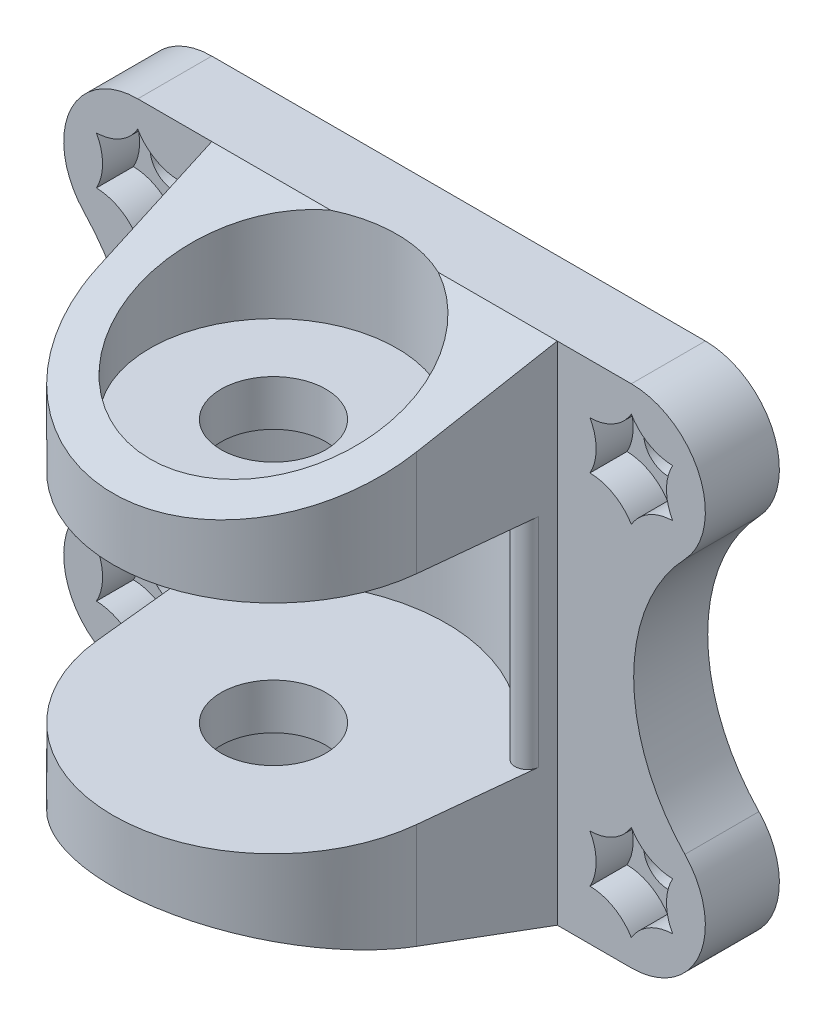
SolidWorks part; units mm, degrees
ref_plane "Front Plane" through (0, 0, 0) normal (0, 0, 1) x (1, 0, 0)
ref_plane "Top Plane" through (0, 0, 0) normal (0, 1, 0) x (1, 0, 0)
ref_plane "Right Plane" through (0, 0, 0) normal (1, 0, 0) x (0, 0, -1)
sketch "Sketch1" plane through (0, 0, 0) normal (0, 1, 0) x (1, 0, 0)
  line L0 (-12.931, -1.3372) -> (-14, 9)
  line L1 (-14, 9) -> (-14, 15)
  line L2 (-14, 15) -> (14, 15)
  line L3 (12.931, -1.3372) -> (14, 9)
  line L4 (14, 9) -> (14, 15)
  circle A0 centre (0, 0) radius 4.25
  arc A1 (-12.931, -1.3372) -> (12.931, -1.3372) centre (0, 0) ccw
  dimension "D1" = 8.5
  dimension "D3" = 13
  dimension "D2" = 15
  dimension "D4" = 28
  dimension "D5" = 6
extrude "Boss-Extrude1" add sketch "Sketch1" along normal mid plane 41
sketch "Sketch2" plane through (0, 0, 0) normal (1, 0, 0) x (0, 0, -1)
  line L0 (0, 0) -> (0, 31.6961) construction
  line L2 (-14, 8.8) -> (0, 8.8)
  line L3 (-14, 8.8) -> (-14, -8.8)
  line L4 (-14, -8.8) -> (0, -8.8)
  line L5 (0, 8.8) -> (0, -8.8)
  dimension "D1" = 17.6
  dimension "D2" = 28
revolve "Cut-Revolve1" cut sketch "Sketch2" angle 360 about L0
sketch "Sketch3" plane through (14, 0, 0) normal (1, 0, 0) x (0, 0, -1)
  line L0 (9, 20.5) -> (-13, 13.8)
  line L1 (-13, 13.8) -> (-13, 20.5)
  line L2 (-13, 20.5) -> (9, 20.5)
  line L3 (-13, -13.8) -> (9, -20.5)
  line L4 (-13, -8.8) -> (-13, -20.5) construction
  line L5 (9, -20.5) -> (-13, -20.5)
  line L6 (-13, -20.5) -> (-13, -13.8)
  line L7 (-1.3372, -8.8) -> (-13, -8.8) construction
  line L8 (-13, 20.5) -> (-13, 8.8) construction
  line L9 (-13, 8.8) -> (-1.3372, 8.8) construction
  dimension "D1" = 5
  dimension "D2" = 5
extrude "Cut-Extrude1" cut sketch "Sketch3" against normal through all
sketch "Sketch7" plane through (0, 0, -15) normal (0, 0, -1) x (-1, 0, 0)
  line L0 (20, 20.5) -> (14, 20.5)
  line L1 (14, 20.5) -> (14, -20.5)
  line L2 (14, 20.5) -> (14, -20.5) construction
  line L3 (14, -20.5) -> (20, -20.5)
  line L4 (-20, -20.5) -> (-14, -20.5)
  line L5 (-20, 20.5) -> (-14, 20.5)
  line L6 (-14, 20.5) -> (-14, -20.5) construction
  line L7 (-14, 20.5) -> (-14, -20.5)
  arc A0 (-20, 20.5) -> (-24.3401, 10.3571) centre (-20, 14.5) ccw
  arc A1 (-24.3401, -10.3571) -> (-20, -20.5) centre (-20, -14.5) ccw
  arc A2 (-24.3401, -10.3571) -> (-24.3401, 10.3571) centre (-35.1905, 0) ccw
  arc A3 (20, -20.5) -> (24.3401, -10.3571) centre (20, -14.5) ccw
  arc A4 (24.3401, 10.3571) -> (20, 20.5) centre (20, 14.5) ccw
  arc A5 (24.3401, 10.3571) -> (24.3401, -10.3571) centre (35.1905, 0) ccw
  circle A6 centre (-20, 14.5) radius 1
  circle A7 centre (-20, -14.5) radius 1
  circle A8 centre (20, -14.5) radius 1
  circle A9 centre (20, 14.5) radius 1
  dimension "D2" = 12
  dimension "D3" = 30
  dimension "D4" = 2
  dimension "D1" = 12
extrude "Boss-Extrude2" add sketch "Sketch7" against normal blind 6
sketch "Sketch8" plane through (0, 0, -9) normal (0, 0, 1) x (1, 0, 0)
  line L1 (-17.15, 12.8546) -> (-17.15, 16.1454)
  line L2 (-17.15, 16.1454) -> (-20, 17.7909)
  line L3 (-20, 17.7909) -> (-22.85, 16.1454)
  line L4 (-22.85, 16.1454) -> (-22.85, 12.8546)
  line L5 (-22.85, 12.8546) -> (-20, 11.2091)
  line L6 (-20, 11.2091) -> (-17.15, 12.8546)
  line L7 (-17.15, -12.8546) -> (-20, -11.2091)
  line L8 (-20, -11.2091) -> (-22.85, -12.8546)
  line L9 (-22.85, -12.8546) -> (-22.85, -16.1454)
  line L10 (-22.85, -16.1454) -> (-20, -17.7909)
  line L11 (-20, -17.7909) -> (-17.15, -16.1454)
  line L12 (-17.15, -16.1454) -> (-17.15, -12.8546)
  line L13 (22.85, -12.8546) -> (20, -11.2091)
  line L14 (20, -11.2091) -> (17.15, -12.8546)
  line L15 (17.15, -12.8546) -> (17.15, -16.1454)
  line L16 (17.15, -16.1454) -> (20, -17.7909)
  line L17 (20, -17.7909) -> (22.85, -16.1454)
  line L18 (22.85, -16.1454) -> (22.85, -12.8546)
  line L19 (22.85, 12.8546) -> (22.85, 16.1454)
  line L20 (22.85, 16.1454) -> (20, 17.7909)
  line L21 (20, 17.7909) -> (17.15, 16.1454)
  line L22 (17.15, 16.1454) -> (17.15, 12.8546)
  line L23 (17.15, 12.8546) -> (20, 11.2091)
  line L24 (20, 11.2091) -> (22.85, 12.8546)
  circle A0 centre (-20, 14.5) radius 2.85 construction
  circle A1 centre (-20, -14.5) radius 2.85 construction
  circle A2 centre (20, -14.5) radius 2.85 construction
  circle A3 centre (20, 14.5) radius 2.85 construction
  dimension "D1" = 5.7
extrude "Cut-Extrude6" cut sketch "Sketch8" against normal blind 3
sketch "Sketch4" plane through (0, 0, -15) normal (0, 0, -1) x (-1, 0, 0)
  line L0 (-20, 14.5) -> (20, -14.5) construction
  circle A0 centre (-20, 14.5) radius 2
  circle A1 centre (20, 14.5) radius 2
  circle A2 centre (-20, -14.5) radius 2
  circle A3 centre (20, -14.5) radius 2
  dimension "D3" = 4
  dimension "D4" = 40
  dimension "D5" = 29
extrude "Cut-Extrude2" cut sketch "Sketch4" against normal blind 7
sketch "Sketch5" plane through (0, 20.5, 0) normal (0, 1, 0) x (1, 0, 0)
  circle A0 centre (0, 0) radius 10
  dimension "D1" = 20
extrude "Cut-Extrude3" cut sketch "Sketch5" against normal blind 8
sketch "Sketch6" plane through (0, -20.5, 0) normal (0, -1, 0) x (1, 0, 0)
  circle A0 centre (0, 0) radius 10 construction
  circle A1 centre (0, 0) radius 10
extrude "Cut-Extrude4" cut sketch "Sketch6" against normal blind 8
fillet "Fillet1" radius 1 2 edges at (13.4655, 0, -3.8314) (-13.4655, 0, -3.8314)
sketch "Sketch9" plane through (0, 0, -9) normal (0, 0, 1) x (1, 0, 0)
  line L0 (-22.85, 12.8546) -> (-20, 11.2091) construction
  line L1 (-20, 18.3682) -> (-23.35, 16.4341) construction
  line L2 (-23.35, 16.4341) -> (-23.35, 12.5659) construction
  line L3 (-23.35, 12.5659) -> (-20, 10.6318) construction
  line L4 (-20, 10.6318) -> (-16.65, 12.5659) construction
  line L5 (-16.65, 12.5659) -> (-16.65, 16.4341) construction
  line L6 (-16.65, 16.4341) -> (-20, 18.3682) construction
  line L7 (-22.85, 16.1454) -> (-22.85, 12.8546) construction
  line L8 (-20, 17.7909) -> (-22.85, 16.1454) construction
  line L9 (-17.15, 16.1454) -> (-20, 17.7909) construction
  line L10 (-17.15, 12.8546) -> (-17.15, 16.1454) construction
  line L11 (-20, 11.2091) -> (-17.15, 12.8546) construction
  circle A0 centre (-20, 14.5) radius 3.35 construction
  arc A1 (-23.35, 16.4341) -> (-23.35, 12.5659) centre (-26.8408, 14.5) cw
  arc A2 (-23.35, 16.4341) -> (-20, 18.3682) centre (-23.4204, 20.4243) ccw
  arc A3 (-20, 18.3682) -> (-16.65, 16.4341) centre (-16.5796, 20.4243) ccw
  arc A4 (-16.65, 16.4341) -> (-16.65, 12.5659) centre (-13.1592, 14.5) ccw
  arc A5 (-16.65, 12.5659) -> (-20, 10.6318) centre (-16.5796, 8.5757) ccw
  arc A6 (-20, 10.6318) -> (-23.35, 12.5659) centre (-23.4204, 8.5757) ccw
  dimension "D1" = 6.7
extrude "Cut-Extrude7" cut sketch "Sketch9" against normal up to surface (3 mm away) up to face at (-18, 14.5, -12)
pattern_linear "LPattern1" count 2 spacing 40 along (1, 0, 0) count 2 spacing 29 along (0, -1, 0) of "Cut-Extrude7"
